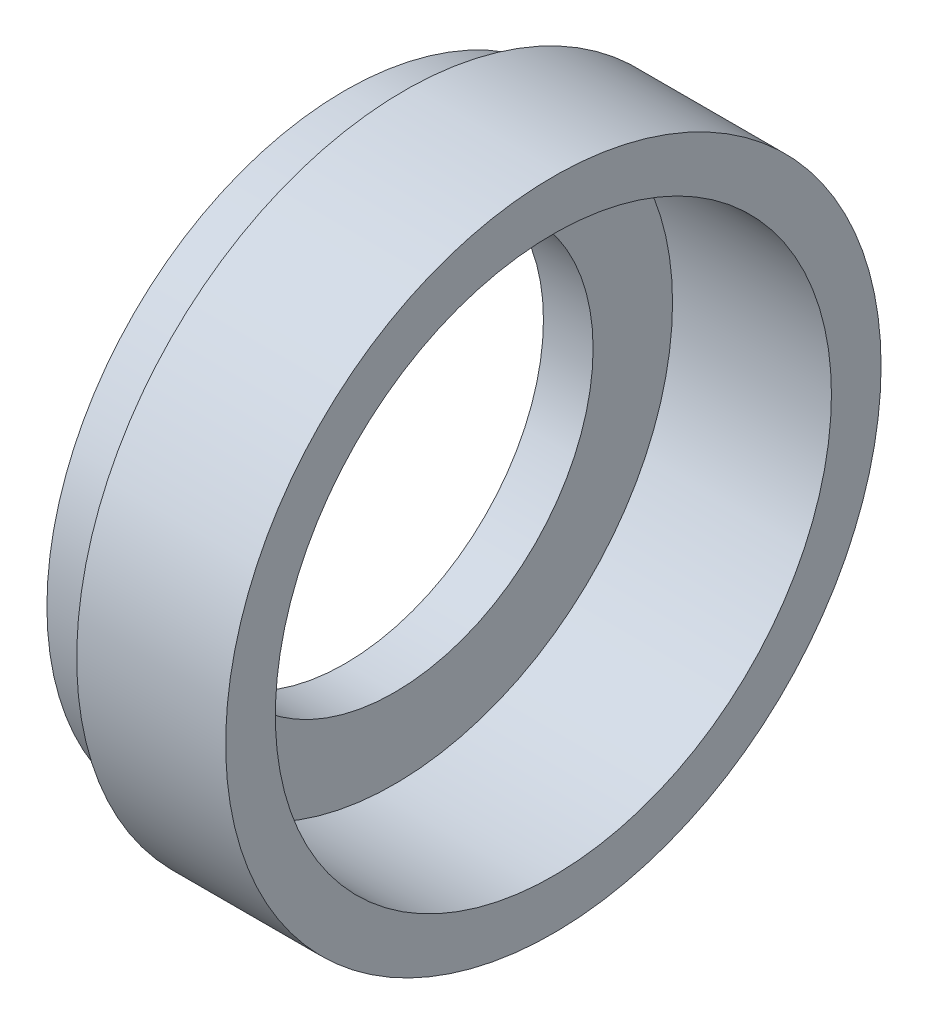
SolidWorks part; units mm, degrees
material "AISI 1020 Сталь, холоднокатаная"
ref_plane "Спереди" through (0, 0, 0) normal (0, 0, 1) x (1, 0, 0)
ref_plane "Сверху" through (0, 0, 0) normal (0, 1, 0) x (1, 0, 0)
ref_plane "Справа" through (0, 0, 0) normal (1, 0, 0) x (0, 0, -1)
sketch "Эскиз1" plane through (0, 0, 0) normal (0, 0, 1) x (1, 0, 0)
  line L0 (0, 0) -> (-27.2732, 0) construction
  line L1 (0, 16.5) -> (0, 14)
  line L2 (0, 14) -> (-8, 14)
  line L3 (-8, 14) -> (-8, 10)
  line L4 (-8, 10) -> (-10.5, 10)
  line L5 (-10.5, 10) -> (-10.5, 15)
  line L6 (-10.5, 15) -> (-7.5, 15)
  line L7 (-7.5, 15) -> (-7.5, 16.5)
  line L8 (-7.5, 16.5) -> (0, 16.5)
  dimension "D1" = 28
  dimension "D2" = 20
  dimension "D3" = 33
  dimension "D4" = 30
  dimension "D5" = 3
  dimension "D6" = 8
  dimension "D7" = 7.5
revolve "Повернуть1" add sketch "Эскиз1" angle 360 about L0
